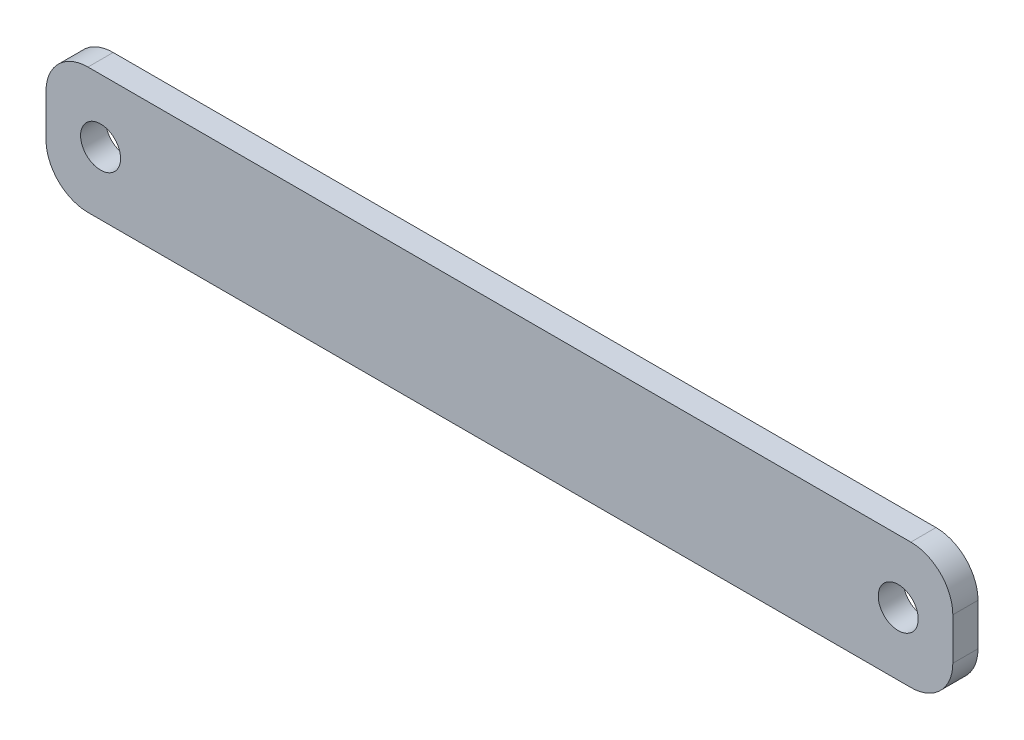
SolidWorks part; units mm, degrees
material "Balsa"
ref_plane "Alzado" through (0, 0, 0) normal (0, 0, 1) x (1, 0, 0)
ref_plane "Planta" through (0, 0, 0) normal (0, 1, 0) x (1, 0, 0)
ref_plane "Vista lateral" through (0, 0, 0) normal (1, 0, 0) x (0, 0, -1)
sketch "Croquis1" plane through (0, 0, 0) normal (0, 0, 1) x (1, 0, 0)
  line L0 (0, 7.5) -> (108, 7.5) construction
  line L1 (5, 0) -> (103, 0)
  line L2 (0, 5) -> (0, 10)
  line L3 (5, 15) -> (103, 15)
  line L4 (108, 5) -> (108, 10)
  line L5 (54, 15) -> (54, 0) construction
  arc A0 (103, 0) -> (108, 5) centre (103, 5) ccw
  arc A1 (103, 15) -> (108, 10) centre (103, 10) cw
  arc A2 (5, 0) -> (0, 5) centre (5, 5) cw
  arc A3 (0, 10) -> (5, 15) centre (5, 10) cw
  circle A4 centre (101.5, 7.5) radius 2.3813
  circle A5 centre (6.5, 7.5) radius 2.3813
  point P13 (108, 15)
  point P16 (0, 0)
  point P19 (0, 15)
  dimension "D3" = 5
  dimension "D4" = 4.7625
  dimension "D1" = 108
  dimension "D2" = 15
  dimension "D5" = 95
extrude "Saliente-Extruir1" add sketch "Croquis1" along normal blind 3
